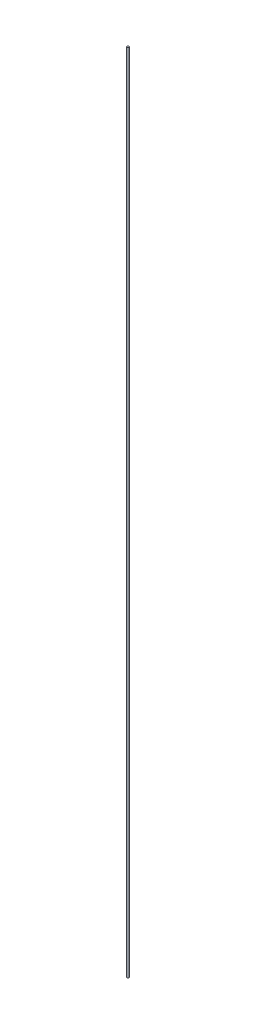
SolidWorks part; units mm, degrees
material "Hexcel AS4C (3000 Filaments)"
ref_plane "Front Plane" through (0, 0, 0) normal (0, 0, 1) x (1, 0, 0)
ref_plane "Top Plane" through (0, 0, 0) normal (0, 1, 0) x (1, 0, 0)
ref_plane "Right Plane" through (0, 0, 0) normal (1, 0, 0) x (0, 0, -1)
sketch "Sketch2" plane through (0, 0, 0) normal (0, 1, 0) x (1, 0, 0)
  circle A0 centre (0, 0) radius 1.27
  dimension "D1" = 2.54
extrude "Boss-Extrude3" add sketch "Sketch2" along normal blind 977.9
